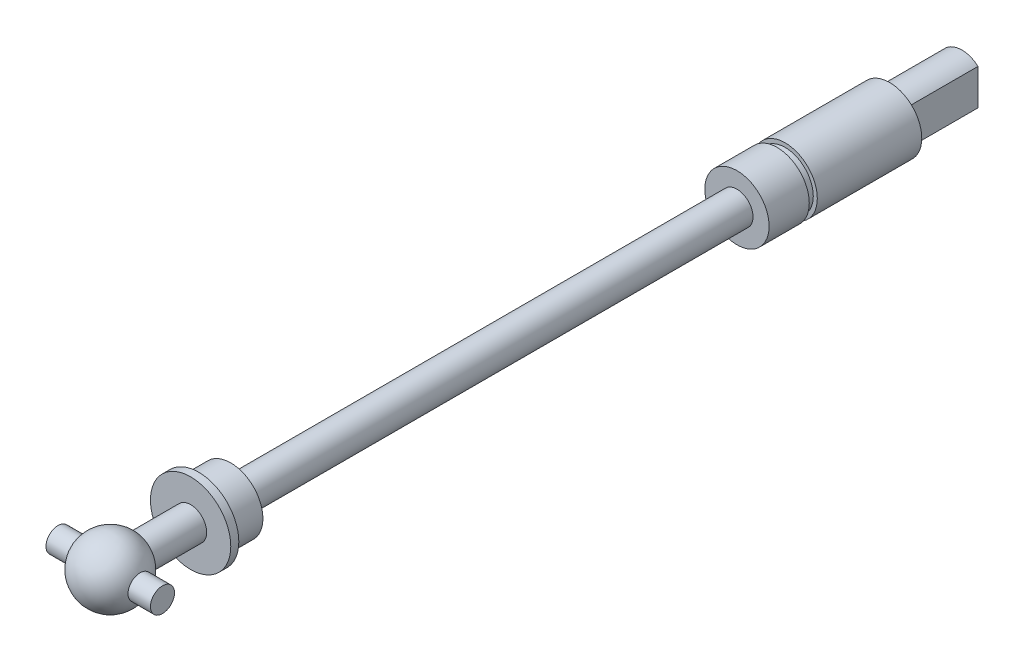
SolidWorks part; units mm, degrees
material "AISI 1020"
ref_plane "Front Plane" through (0, 0, 0) normal (0, 0, 1) x (1, 0, 0)
ref_plane "Top Plane" through (0, 0, 0) normal (0, 1, 0) x (1, 0, 0)
ref_plane "Right Plane" through (0, 0, 0) normal (1, 0, 0) x (0, 0, -1)
sketch "Sketch1" plane through (0, 0, 0) normal (1, 0, 0) x (0, 0, -1)
  line L0 (0, 0) -> (110, 0) construction
  line L1 (7.4641, 2) -> (14, 2)
  line L2 (14, 2) -> (14, 5)
  line L3 (14, 5) -> (15, 5)
  line L4 (15, 5) -> (15, 4)
  line L5 (15, 4) -> (19, 4)
  line L6 (19, 4) -> (19, 2)
  line L7 (19, 2) -> (82, 2)
  line L8 (82, 2) -> (82, 4)
  line L9 (82, 4) -> (87, 4)
  line L10 (87, 4) -> (87, 3.5)
  line L11 (87, 3.5) -> (88, 3.5)
  line L12 (88, 3.5) -> (88, 4)
  line L13 (88, 4) -> (101, 4)
  line L14 (101, 4) -> (101, 3)
  line L15 (101, 3) -> (110, 3)
  line L16 (110, 3) -> (110, 0)
  line L17 (0, 0) -> (110, 0)
  arc A0 (7.4641, 2) -> (0, 0) centre (4, 0) ccw
  dimension "D2" = 8
  dimension "D1" = 110
  dimension "D3" = 10
  dimension "D4" = 2
  dimension "D5" = 2
  dimension "D6" = 4
  dimension "D7" = 5
  dimension "D8" = 4
  dimension "D9" = 4
  dimension "D10" = 3
  dimension "D11" = 3.5
  dimension "D12" = 1
  dimension "D13" = 4
  dimension "D15" = 5
  dimension "D16" = 14
  dimension "D17" = 1
  dimension "D18" = 9
revolve "Revolve1" add sketch "Sketch1" angle 360 about L0
sketch "Sketch2" plane through (0, 0, -110) normal (0, 0, -1) x (-1, 0, 0)
  line L0 (0, -3) -> (0, 3) construction
  line L1 (2, -2.2361) -> (2, 2.2361)
  line L2 (-2, -2.2361) -> (-2, 2.2361)
  line L3 (-2, -3) -> (-2, 3) construction
  line L4 (2, -3) -> (2, 3) construction
  circle A2 centre (0, 0) radius 3
  circle A3 centre (0, 0) radius 3
  circle M3 centre (0, 0) radius 3
  dimension "D1" = 0
  dimension "D2" = 2
  dimension "D3" = 2
extrude "Cut-Extrude1" cut sketch "Sketch2" against normal up to surface (9 mm away) contours L2 M3 | L1 M3 up to face at (4, 0, -101)
sketch "Sketch3" plane through (0, 0, 0) normal (1, 0, 0) x (0, 0, -1)
  circle A0 centre (4, 0) radius 4
  circle A1 centre (4, 0) radius 1.5
  dimension "D2" = 3
extrude "Boss-Extrude1" add sketch "Sketch3" along normal mid plane 13 contours A1
